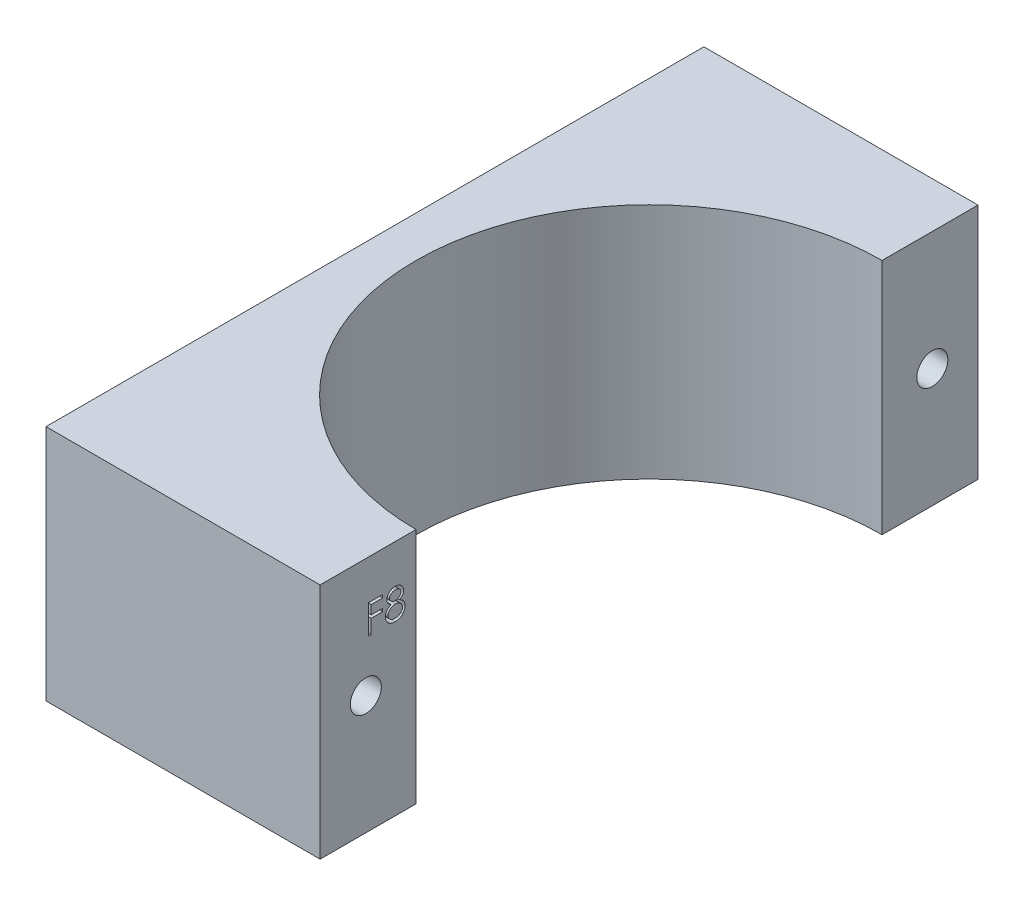
SolidWorks part; units mm, degrees
ref_plane "Front Plane" through (0, 0, 0) normal (0, 0, 1) x (1, 0, 0)
ref_plane "Top Plane" through (0, 0, 0) normal (0, 1, 0) x (1, 0, 0)
ref_plane "Right Plane" through (0, 0, 0) normal (1, 0, 0) x (0, 0, -1)
sketch "Sketch1" plane through (0, 0, 0) normal (0, 1, 0) x (1, 0, 0)
  line L0 (-46.9983, 32.5286) -> (-46.9983, -39.4714)
  line L1 (-46.9983, -39.4714) -> (-16.9983, -39.4714)
  line L2 (-16.9983, -39.4714) -> (-16.9983, -28.9714)
  line L3 (-46.9983, 32.5286) -> (-16.9983, 32.5286)
  line L4 (-16.9983, 32.5286) -> (-16.9983, 22.0286)
  arc A0 (-16.9983, 22.0286) -> (-16.9983, -28.9714) centre (-16.9983, -3.4714) ccw
  dimension "D1" = 72
  dimension "D2" = 30
  dimension "D3" = 30
  dimension "D4" = 10.5
  dimension "D5" = 10.5
extrude "Boss-Extrude1" add sketch "Sketch1" along normal blind 26
sketch "Sketch2" plane through (-16.9983, 0, 0) normal (1, 0, 0) x (0, 0, -1)
  line L0 (-34.4714, 26) -> (-34.4714, 0) construction
  line L1 (-39.4714, 26) -> (-28.9714, 26) construction
  line L2 (-39.4714, 0) -> (-28.9714, 0) construction
  line L3 (27.5286, 26) -> (27.5286, 0) construction
  line L4 (22.0286, 26) -> (32.5286, 26) construction
  line L5 (22.0286, 0) -> (32.5286, 0) construction
  line L6 (-39.4714, 26) -> (-39.4714, 0) construction
  line L7 (32.5286, 26) -> (32.5286, 0) construction
  circle A0 centre (-34.4714, 13) radius 1.7
  circle A1 centre (27.5286, 13) radius 1.7
  dimension "D1" = 5
  dimension "D2" = 5
extrude "Cut-Extrude1" cut sketch "Sketch2" against normal through all
sketch "Sketch3" plane through (-16.9983, 0, 0) normal (1, 0, 0) x (0, 0, -1)
  text T0 "F8"
extrude "Cut-Extrude2" cut sketch "Sketch3" against normal blind 1
